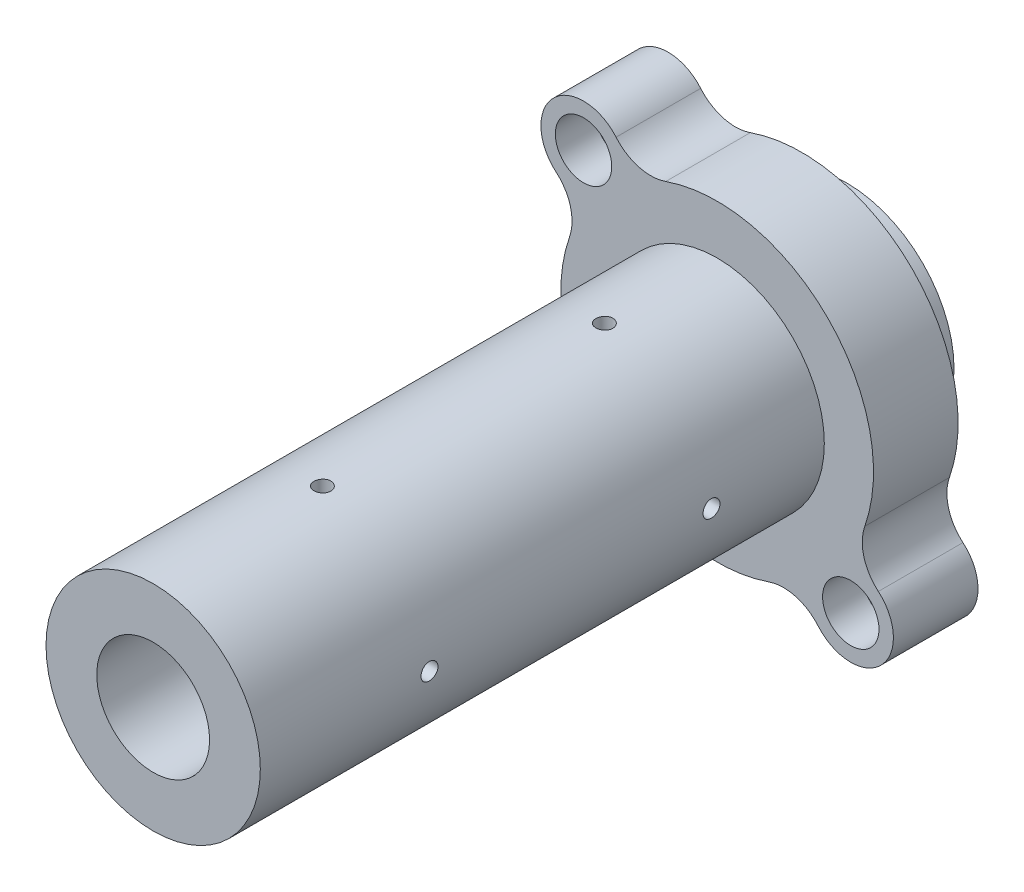
SolidWorks part; units mm, degrees
ref_plane "FRONT" through (0, 0, 0) normal (0, 0, 1) x (1, 0, 0)
ref_plane "TOP" through (0, 0, 0) normal (0, 1, 0) x (1, 0, 0)
ref_plane "RIGHT" through (0, 0, 0) normal (1, 0, 0) x (0, 0, -1)
ref_plane "Plan1" through (0, 0, 838.2) normal (0, 0, 1) x (1, 0, 0)
sketch "Esquisse1" plane through (0, 0, 838.2) normal (0, 0, 1) x (1, 0, 0)
  arc A0 (-9.1186, 26.1774) -> (-17.9219, 28.5774) centre (-11.7713, 33.7926) cw
  arc A1 (-17.9219, 28.5774) -> (-28.5774, 17.9219) centre (-23.6881, 23.6881) ccw
  arc A2 (-28.5774, 17.9219) -> (-26.1774, 9.1186) centre (-33.7926, 11.7713) cw
  arc A3 (-26.1774, 9.1186) -> (9.1186, -26.1774) centre (0, 0) ccw
  arc A4 (9.1186, -26.1774) -> (17.9219, -28.5774) centre (11.7713, -33.7926) cw
  arc A5 (17.9219, -28.5774) -> (28.5774, -17.9219) centre (23.6881, -23.6881) ccw
  arc A6 (28.5774, -17.9219) -> (26.1774, -9.1186) centre (33.7926, -11.7713) cw
  arc A7 (26.1774, -9.1186) -> (-9.1186, 26.1774) centre (0, 0) ccw
  circle A8 centre (23.6881, -23.6881) radius 2.65
  circle A9 centre (-23.6881, 23.6881) radius 2.65
  dimension "D1" = 67
extrude "Boss.-Extru.1" add sketch "Esquisse1" against normal blind 15
sketch "Esquisse9" plane through (0, 0, 838.2) normal (0, 0, 1) x (1, 0, 0)
  circle A0 centre (0, 0) radius 19
extrude "Boss.-Extru.4" add sketch "Esquisse9" along normal blind 100 and the other way blind 23
sketch "Esquisse12" plane through (0, 0, 938.2) normal (0, 0, 1) x (1, 0, 0)
  circle A0 centre (0, 0) radius 10
extrude "Enlèv. mat.-Extru.2" cut sketch "Esquisse12" against normal through all
sketch "Esquisse13" plane through (0, 0, 838.2) normal (0, 0, 1) x (1, 0, 0)
  circle A0 centre (-23.6881, 23.6881) radius 5
  circle A1 centre (23.6881, -23.6881) radius 5
extrude "Enlèv. mat.-Extru.3" cut sketch "Esquisse13" against normal blind 7
sketch "Esquisse14" plane through (0, 0, 0) normal (0, 1, 0) x (1, 0, 0)
  line L0 (0, -953.6616) -> (0, -802.1089) construction
  line L1 (-55, -838.2) -> (55, -838.2) construction
  circle A0 centre (0, -858.2) radius 1.5
  circle A1 centre (0, -908.2) radius 1.5
  dimension "D1" = 20
  dimension "D2" = 50
extrude "Enlèv. mat.-Extru.4" cut sketch "Esquisse14" against normal through all both and the other way through all
sketch "Esquisse15" plane through (0, 0, 0) normal (1, 0, 0) x (0, 0, -1)
  line L0 (-972.889, 0) -> (-803.6419, 0) construction
  line L1 (-838.2, 55) -> (-838.2, -55) construction
  circle A0 centre (-858.2, 0) radius 1.5
  circle A1 centre (-908.2, 0) radius 1.5
  dimension "D1" = 20
  dimension "D2" = 50
extrude "Enlèv. mat.-Extru.5" cut sketch "Esquisse15" against normal through all both and the other way through all
